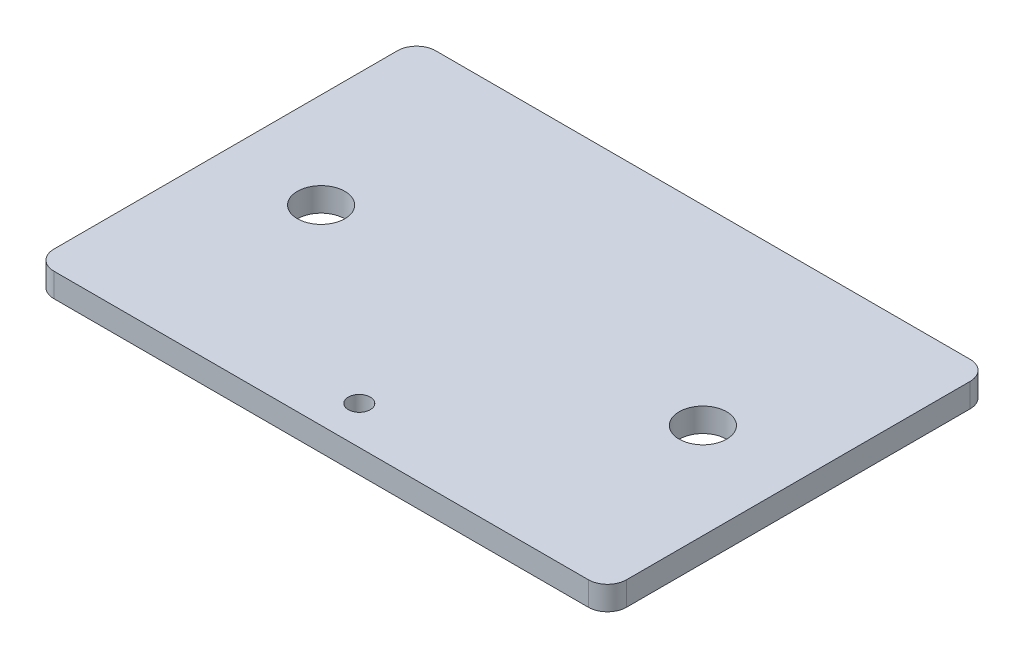
SolidWorks part; units mm, degrees
ref_plane "Front Plane" through (0, 0, 0) normal (0, 0, 1) x (1, 0, 0)
ref_plane "Top Plane" through (0, 0, 0) normal (0, 1, 0) x (1, 0, 0)
ref_plane "Right Plane" through (0, 0, 0) normal (1, 0, 0) x (0, 0, -1)
sketch "Sketch1" plane through (0, 0, 0) normal (0, 1, 0) x (1, 0, 0)
  line L0 (0, 0) -> (0, 48.7112) construction
  line L1 (38.1, 25.4) -> (-38.1, 25.4)
  line L2 (38.1, 25.4) -> (38.1, -25.4)
  line L3 (38.1, -25.4) -> (-38.1, -25.4)
  line L4 (-38.1, 25.4) -> (-38.1, -25.4)
  line L5 (38.1, 25.4) -> (-38.1, -25.4) construction
  line L6 (38.1, -25.4) -> (-38.1, 25.4) construction
  circle A0 centre (-25.4, 0) radius 3.1623
  circle A1 centre (25.4, 0) radius 3.1623
  circle A2 centre (0, -20.32) radius 1.4605
  point P0 (0, 0)
  point P14 (0, 0)
  dimension "D3" = 6.3246
  dimension "D5" = 2.921
  dimension "D1" = 76.2
  dimension "D2" = 50.8
  dimension "D4" = 50.8
  dimension "D6" = 5.08
extrude "Boss-Extrude1" add sketch "Sketch1" along normal mid plane 3.175
fillet "Fillet1" radius 2.54 4 edges at (-38.1, 0, -25.4) (38.1, 0, -25.4) (38.1, 0, 25.4) (-38.1, 0, 25.4)
